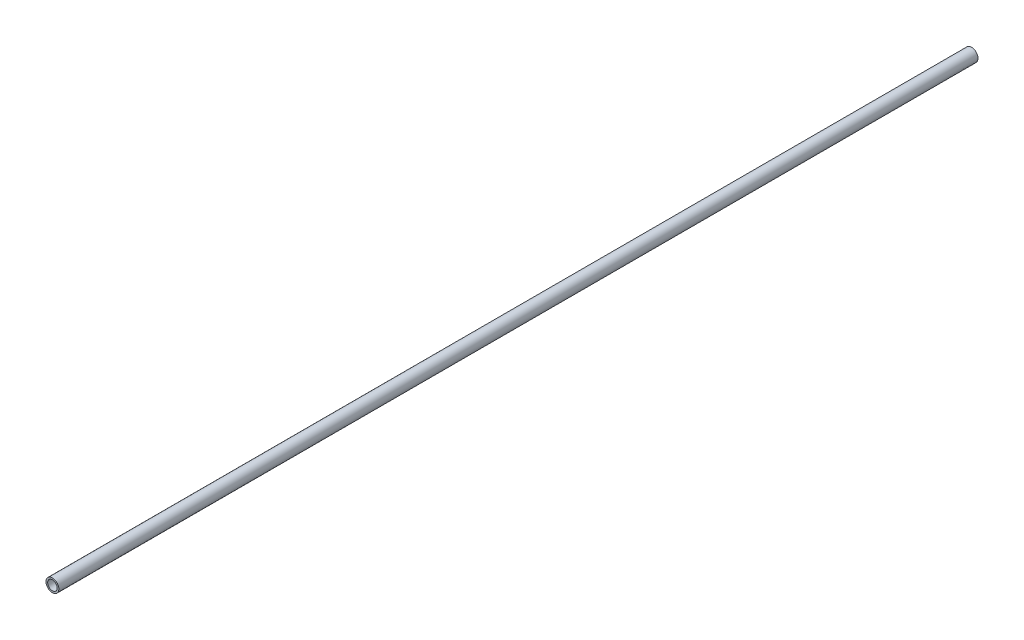
SolidWorks part; units mm, degrees
ref_plane "Front Plane" through (0, 0, 0) normal (0, 0, 1) x (1, 0, 0)
ref_plane "Top Plane" through (0, 0, 0) normal (0, 1, 0) x (1, 0, 0)
ref_plane "Right Plane" through (0, 0, 0) normal (1, 0, 0) x (0, 0, -1)
sketch "Sketch1" plane through (0, 0, 0) normal (0, 0, 1) x (1, 0, 0)
  circle A0 centre (0, 0) radius 10.668
  dimension "Pipe OD" = 21.336
extrude "Extrude-Thin1" add sketch "Sketch1" along normal mid plane 1524 thin thin type one direction reverse wall 2.7686
